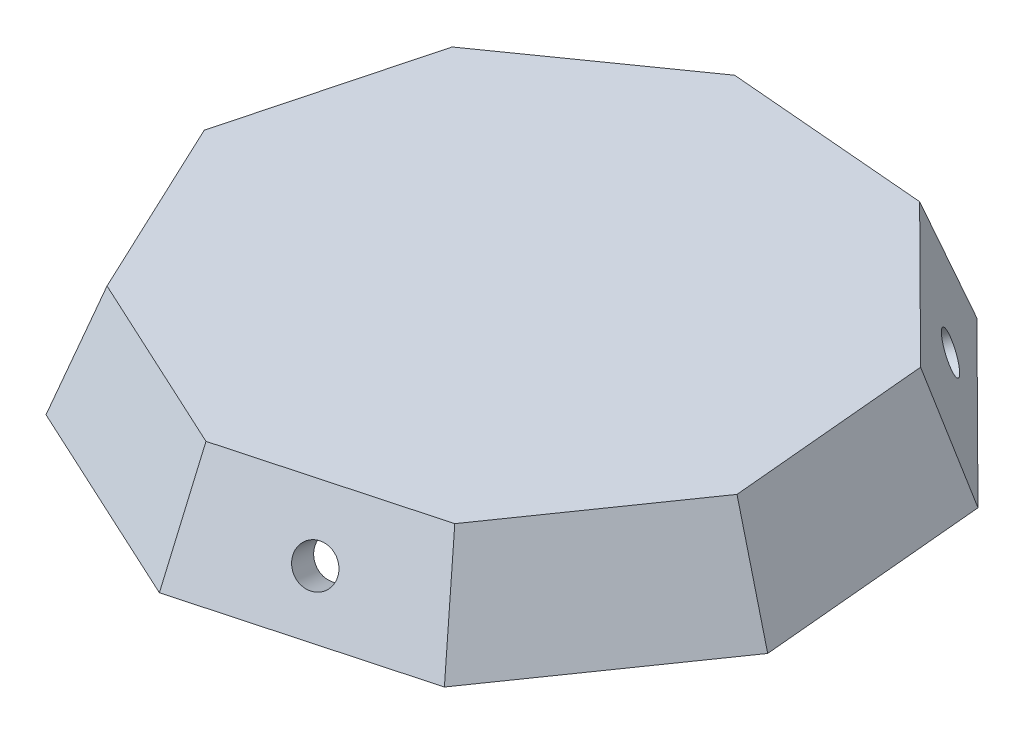
SolidWorks part; units mm, degrees
ref_plane "Front Plane" through (0, 0, 0) normal (0, 0, 1) x (1, 0, 0)
ref_plane "Top Plane" through (0, 0, 0) normal (0, 1, 0) x (1, 0, 0)
ref_plane "Right Plane" through (0, 0, 0) normal (1, 0, 0) x (0, 0, -1)
sketch "Sketch2" plane through (0, 0, 0) normal (0, 1, 0) x (1, 0, 0)
  line L1 (25.7206, -6.8007) -> (24.0745, 11.3232)
  line L2 (24.0745, 11.3232) -> (11.1637, 24.1489)
  line L3 (11.1637, 24.1489) -> (-6.9707, 25.675)
  line L4 (-6.9707, 25.675) -> (-21.8434, 15.1875)
  line L5 (-21.8434, 15.1875) -> (-26.4954, -2.4064)
  line L6 (-26.4954, -2.4064) -> (-18.7498, -18.8743)
  line L7 (-18.7498, -18.8743) -> (-2.231, -26.5107)
  line L8 (-2.231, -26.5107) -> (15.3317, -21.7425)
  line L9 (15.3317, -21.7425) -> (25.7206, -6.8007)
  circle A0 centre (0, 0) radius 25 construction
  dimension "D1" = 50
extrude "Boss-Extrude1" add sketch "Sketch2" along normal blind 10
draft "Draft1" type of draft neutral plane draft angle 20 faces to draft 9 face at (-24.1694, 5, -6.3906) face at (-14.4071, 5, -20.4313) face at (2.0965, 5, -24.9119) face at (17.6191, 5, -17.7361) face at (24.8975, 5, -2.2613) face at (20.5261, 5, 14.2716) face at (-10.4904, 5, 22.6925) face at (-22.6226, 5, 10.6404) face at (6.5503, 5, 24.1266) neutral plane through (0, 10, 0) neutral plane normal (0, 1, 0) parameters "D1"=20
shell "Shell1" thickness 3
sketch "Sketch3" plane through (6.6262, 9.2046, 24.406) normal (0.2462, 0.342, 0.9069) x (0.9692, -0.0869, -0.2304)
  line L0 (-9.4737, -10.7172) -> (11.285, -8.7896) construction
  line L1 (-0.0783, 0.8428) -> (0.9057, -9.7534) construction
  line L2 (-9.1385, 0.0015) -> (8.982, 1.6841) construction
  circle A0 centre (0.4434, -4.7748) radius 1.7
  dimension "D2" = 3.4
  dimension "D1" = 5
extrude "Cut-Extrude1" cut sketch "Sketch3" against normal up to next (3 mm away)
pattern_circular "CirPattern1" count 3 every 120 about axis through (0, 10, 0) along (0, 1, 0) of "Cut-Extrude1"
